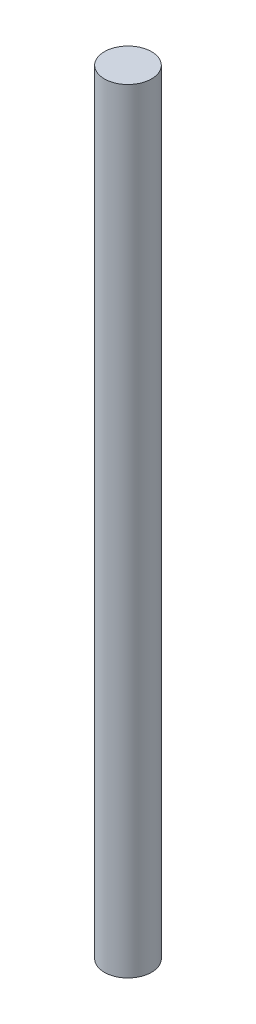
SolidWorks part; units mm, degrees
ref_plane "Front" through (0, 0, 0) normal (0, 0, 1) x (1, 0, 0)
ref_plane "Top" through (0, 0, 0) normal (0, 1, 0) x (1, 0, 0)
ref_plane "Right" through (0, 0, 0) normal (1, 0, 0) x (0, 0, -1)
sketch "Sketch1" plane through (0, 0, 0) normal (0, 1, 0) x (1, 0, 0)
  circle A0 centre (0, 0) radius 1.5875
  dimension "D1" = 3.175
extrude "Boss-Extrude1" add sketch "Sketch1" along normal blind 52.07
